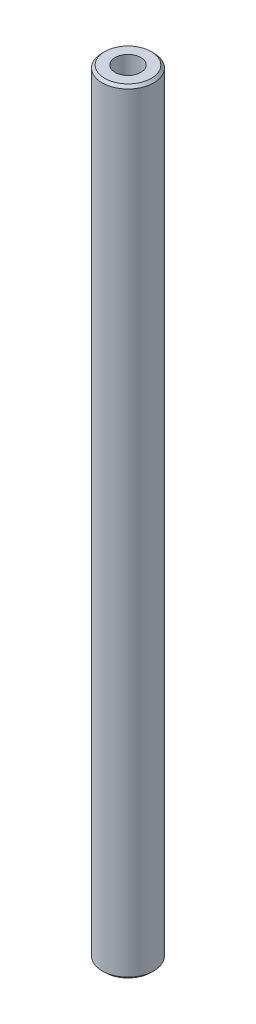
SolidWorks part; units mm, degrees
ref_plane "Face" through (0, 0, 0) normal (0, 0, 1) x (1, 0, 0)
ref_plane "Dessus" through (0, 0, 0) normal (0, 1, 0) x (1, 0, 0)
ref_plane "Droite" through (0, 0, 0) normal (1, 0, 0) x (0, 0, -1)
sketch "Esquisse1" plane through (0, 0, 0) normal (0, 1, 0) x (1, 0, 0)
  circle A0 centre (0, 0) radius 5
  dimension "D1" = 10
extrude "Extrusion1" add sketch "Esquisse1" along normal blind 150
chamfer "Chanfrein1" distance 0.5 angle 45 2 edges at (0, 150, 5) (0, 0, 5)
sketch "Esquisse2" plane through (0, 0, 0) normal (0, -1, 0) x (1, 0, 0)
  circle A0 centre (0, 0) radius 2.5
  dimension "D1" = 5
extrude "Extrusion2" cut sketch "Esquisse2" against normal blind 15
sketch "Esquisse3" plane through (0, 150, 0) normal (0, 1, 0) x (1, 0, 0)
  circle A0 centre (0, 0) radius 2.5
  dimension "D1" = 5
extrude "Extrusion3" cut sketch "Esquisse3" against normal blind 15
